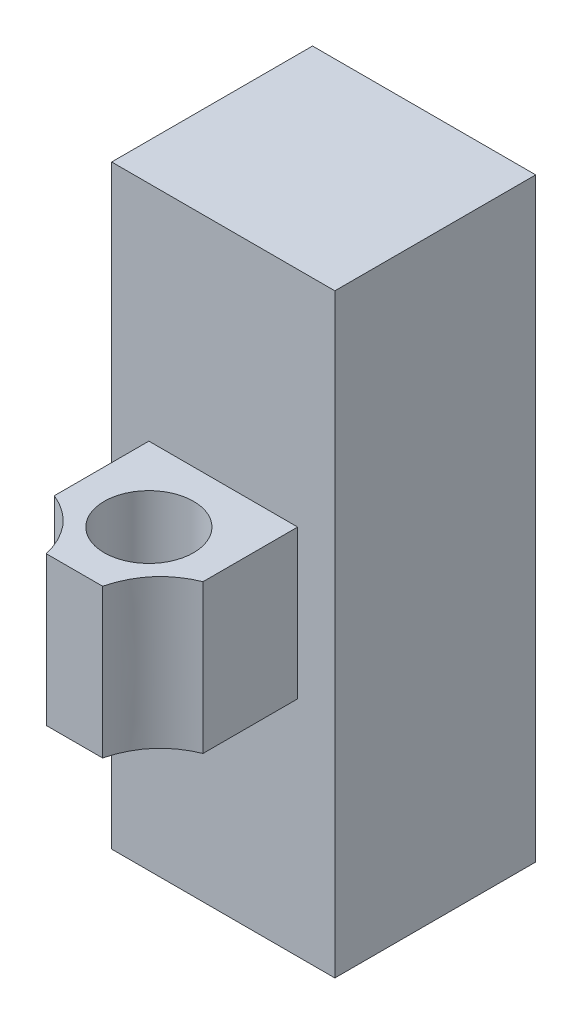
SolidWorks part; units mm, degrees
ref_plane "Front Plane" through (0, 0, 0) normal (0, 0, 1) x (1, 0, 0)
ref_plane "Top Plane" through (0, 0, 0) normal (0, 1, 0) x (1, 0, 0)
ref_plane "Right Plane" through (0, 0, 0) normal (1, 0, 0) x (0, 0, -1)
sketch "Sketch1" plane through (0, 0, 0) normal (0, 0, 1) x (1, 0, 0)
  line L1 (-10, -10) -> (10, -10)
  line L2 (-10, -10) -> (-10, 10)
  line L3 (-10, 10) -> (10, 10)
  line L4 (10, -10) -> (10, 10)
  line L5 (-10, -10) -> (10, 10) construction
  line L6 (-10, 10) -> (10, -10) construction
  point P0 (0, 0)
  dimension "D1" = 20
  dimension "D2" = 20
extrude "Boss-Extrude1" add sketch "Sketch1" along normal blind 20
sketch "Sketch2" plane through (0, 10, 0) normal (0, 1, 0) x (1, 0, 0)
  line L1 (0, 4.405) -> (0, -16.1822) construction
  line L2 (-11.1854, -10) -> (12.0211, -10) construction
  circle A1 centre (0, -10) radius 6
  dimension "D1" = 12
extrude "Cut-Extrude1" cut sketch "Sketch2" against normal through all contours A1
sketch "Sketch3" plane through (0, 10, 0) normal (0, 1, 0) x (1, 0, 0)
  line L0 (-10, -20) -> (-10, 0) construction
  line L1 (10, -20) -> (-10, -20) construction
  line L2 (0, 0.5168) -> (0, -23.6784) construction
  line L3 (-10, -12.7143) -> (-10, -20)
  line L4 (-10, -20) -> (-3.7883, -20)
  line L5 (10, -12.7143) -> (10, -20)
  line L6 (10, -20) -> (3.7883, -20)
  spline S0 degree 2 poles (-10, -12.7143) (-5.1127, -14.7566) (-3.7883, -20) knots 0 0 0 1 1 1
  spline S1 degree 2 poles (10, -12.7143) (5.1127, -14.7566) (3.7883, -20) knots 0 0 0 1 1 1
extrude "Cut-Extrude2" cut sketch "Sketch3" against normal through all
sketch "Sketch4" plane through (0, 0, 0) normal (0, 0, -1) x (-1, 0, 0)
  line L1 (15, -40) -> (-15, -40)
  line L2 (15, -40) -> (15, 40)
  line L3 (15, 40) -> (-15, 40)
  line L4 (-15, -40) -> (-15, 40)
  line L5 (15, -40) -> (-15, 40) construction
  line L6 (15, 40) -> (-15, -40) construction
  point P0 (0, 0)
  dimension "D1" = 80
  dimension "D2" = 30
extrude "Boss-Extrude2" add sketch "Sketch4" along normal blind 27
